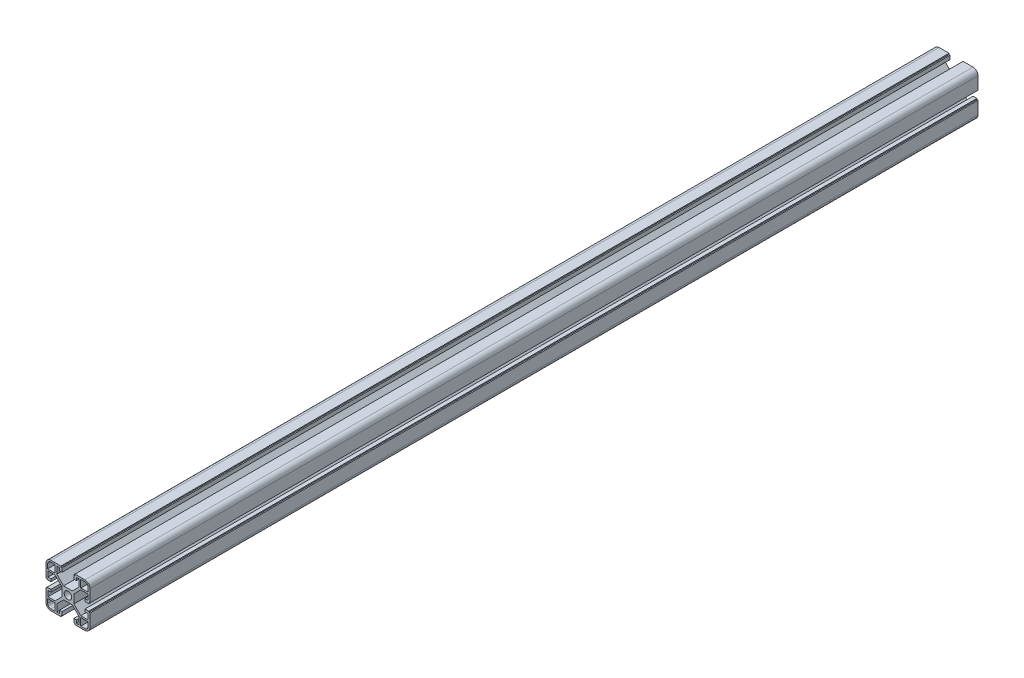
SolidWorks part; units mm, degrees
material "6061-T6 (SS)"
ref_plane "Front Plane" through (0, 0, 0) normal (0, 0, 1) x (1, 0, 0)
ref_plane "Top Plane" through (0, 0, 0) normal (0, 1, 0) x (1, 0, 0)
ref_plane "Right Plane" through (0, 0, 0) normal (1, 0, 0) x (0, 0, -1)
sketch "Sketch1" plane through (0, 0, 0) normal (0, 0, 1) x (1, 0, 0)
  line L0 (3.4, 0) -> (5.5, 0)
  line L1 (10.19, 11.69) -> (4, 5.5)
  line L2 (11.69, 10.19) -> (5.5, 4)
  line L3 (18.2, 10.19) -> (11.69, 10.19)
  line L4 (18.2, 10.19) -> (18.2, 5.2656)
  line L5 (18.2, 5.2656) -> (15.5, 5.2656)
  line L6 (15.5, 5.2656) -> (15.5, 2.9656)
  line L7 (15.5, 2.9656) -> (19, 2.9656)
  line L8 (19, 2.9656) -> (19, 3.9656)
  line L9 (19, 3.9656) -> (20, 3.9656)
  line L10 (20, 3.9656) -> (20, 15.5)
  line L11 (15.5, 20) -> (6.3853, 20)
  line L12 (18.5, 11.69) -> (18.5, 15.5)
  line L13 (15.5, 18.5) -> (11.69, 18.5)
  line L14 (11.69, 11.69) -> (11.69, 18.5)
  line L15 (0, 3.4) -> (0, 5.5)
  line L16 (4, 5.5) -> (0, 5.5)
  line L17 (6.3853, 20) -> (6.3853, 19)
  line L18 (5.5, 0) -> (5.5, 4)
  line L19 (6.3853, 19) -> (5.3853, 19)
  line L20 (5.3853, 19) -> (5.3853, 15.5)
  line L21 (5.3853, 15.5) -> (7.6853, 15.5)
  line L22 (10.19, 11.69) -> (10.19, 18.2)
  line L23 (11.69, 11.69) -> (18.5, 11.69)
  line L24 (7.6853, 18.2) -> (7.6853, 15.5)
  line L25 (10.19, 18.2) -> (7.6853, 18.2)
  arc A0 (20, 15.5) -> (15.5, 20) centre (15.5, 15.5) ccw
  arc A1 (18.5, 15.5) -> (15.5, 18.5) centre (15.5, 15.5) ccw
  arc A2 (3.4, 0) -> (0, 3.4) centre (0, 0) ccw
  dimension "D3" = 4.5
  dimension "D18" = 1.5
  dimension "D9" = 3.4
  dimension "D20" = 1.8
  dimension "D25" = 3
  dimension "D1" = 5.5
  dimension "D2" = 1.5
  dimension "D4" = 14.5
  dimension "D5" = 1.5
  dimension "D6" = 2.1
  dimension "D7" = 2.3
  dimension "D8" = 1.8
  dimension "D10" = 6.81
  dimension "D11" = 2.1
  dimension "D12" = 1
  dimension "D13" = 4.5
  dimension "D14" = 45
  dimension "D15" = 14.5
  dimension "D16" = 1
  dimension "D17" = 1.5
  dimension "D19" = 6.81
  dimension "D21" = 4.5
  dimension "D22" = 2.3
  dimension "D23" = 1
  dimension "D24" = 1
  dimension "D26" = 8.754
  dimension "D27" = 8.754
  dimension "D28" = 4.9244
  dimension "D29" = 2.5047
extrude "Boss-Extrude1" add sketch "Sketch1" along normal blind 810
mirror "Mirror1" about plane through (0, 0, 0) normal (0, 1, 0) of "Boss-Extrude1"
mirror "Mirror2" about plane through (0, 0, 0) normal (1, 0, 0) of "Boss-Extrude1"
mirror "Mirror3" about plane through (0, 0, 0) normal (0, 1, 0) of "Mirror2"
